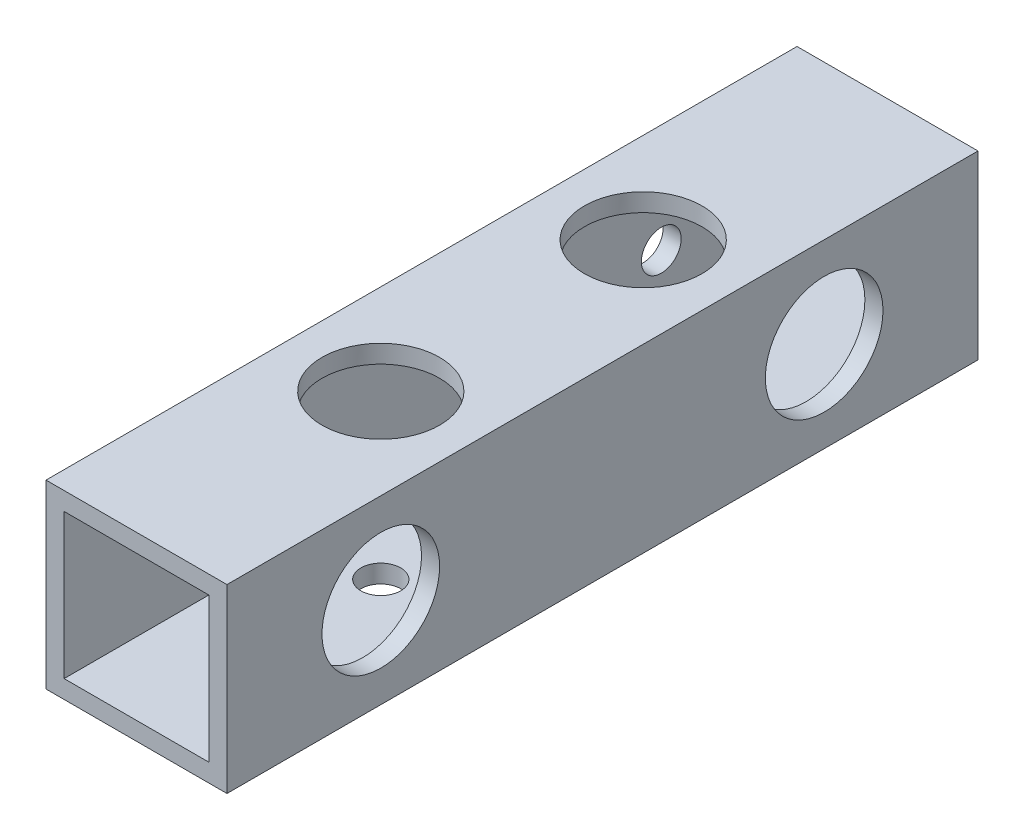
SolidWorks part; units mm, degrees
ref_plane "正面" through (0, 0, 0) normal (0, 0, 1) x (1, 0, 0)
ref_plane "平面" through (0, 0, 0) normal (0, 1, 0) x (1, 0, 0)
ref_plane "右側面" through (0, 0, 0) normal (1, 0, 0) x (0, 0, -1)
sketch "ｽｹｯﾁ1" plane through (0, 0, 0) normal (0, 0, 1) x (1, 0, 0)
  line L1 (-10, 10) -> (10, 10)
  line L2 (-10, 10) -> (-10, -10)
  line L3 (-10, -10) -> (10, -10)
  line L4 (10, 10) -> (10, -10)
  line L5 (-10, 10) -> (10, -10) construction
  line L6 (-10, -10) -> (10, 10) construction
  line L7 (-8, 8) -> (8, 8)
  line L8 (-8, 8) -> (-8, -8)
  line L9 (-8, -8) -> (8, -8)
  line L10 (8, 8) -> (8, -8)
  line L11 (-8, 8) -> (8, -8) construction
  line L12 (-8, -8) -> (8, 8) construction
  point P0 (0, 0)
  point P6 (0, 0)
  dimension "D1" = 20
  dimension "D2" = 20
  dimension "D3" = 16
  dimension "D4" = 16
extrude "ﾎﾞｽ - 押し出し1" add sketch "ｽｹｯﾁ1" along normal blind 83
sketch "ｽｹｯﾁ2" plane through (10, 0, 0) normal (1, 0, 0) x (0, 0, -1)
  line L0 (-83, 0) -> (-66, 0)
  line L1 (-83, -10) -> (-83, 10) construction
  line L2 (0, 0) -> (-17, 0)
  circle A0 centre (-66, 0) radius 2.2
  circle A1 centre (-17, 0) radius 2.2
  dimension "D3" = 4.4
  dimension "D4" = 4.4
  dimension "D1" = 17
  dimension "D2" = 17
extrude "ｶｯﾄ - 押し出し1" cut sketch "ｽｹｯﾁ2" against normal blind 83
sketch "ｽｹｯﾁ3" plane through (10, 0, 0) normal (1, 0, 0) x (0, 0, -1)
  circle A0 centre (-66, 0) radius 6.5
  circle A1 centre (-17, 0) radius 6.5
  dimension "D1" = 13
  dimension "D2" = 13
extrude "ｶｯﾄ - 押し出し2" cut sketch "ｽｹｯﾁ3" against normal blind 3
sketch "ｽｹｯﾁ4" plane through (0, -10, 0) normal (0, -1, 0) x (1, 0, 0)
  line L0 (0, 83) -> (0, 56)
  line L1 (-10, 83) -> (10, 83) construction
  line L2 (0, 0) -> (0, 27)
  line L3 (-10, 0) -> (10, 0) construction
  circle A0 centre (0, 56) radius 2.2
  circle A1 centre (0, 27) radius 2.2
  dimension "D2" = 4.4
  dimension "D4" = 4.4
  dimension "D1" = 27
  dimension "D3" = 27
extrude "ｶｯﾄ - 押し出し3" cut sketch "ｽｹｯﾁ4" against normal through all both and the other way through all
sketch "ｽｹｯﾁ5" plane through (0, 10, 0) normal (0, 1, 0) x (1, 0, 0)
  circle A0 centre (0, -56) radius 6.5
  circle A1 centre (0, -27) radius 6.5
  dimension "D1" = 13
  dimension "D2" = 13
extrude "ｶｯﾄ - 押し出し4" cut sketch "ｽｹｯﾁ5" against normal blind 3
